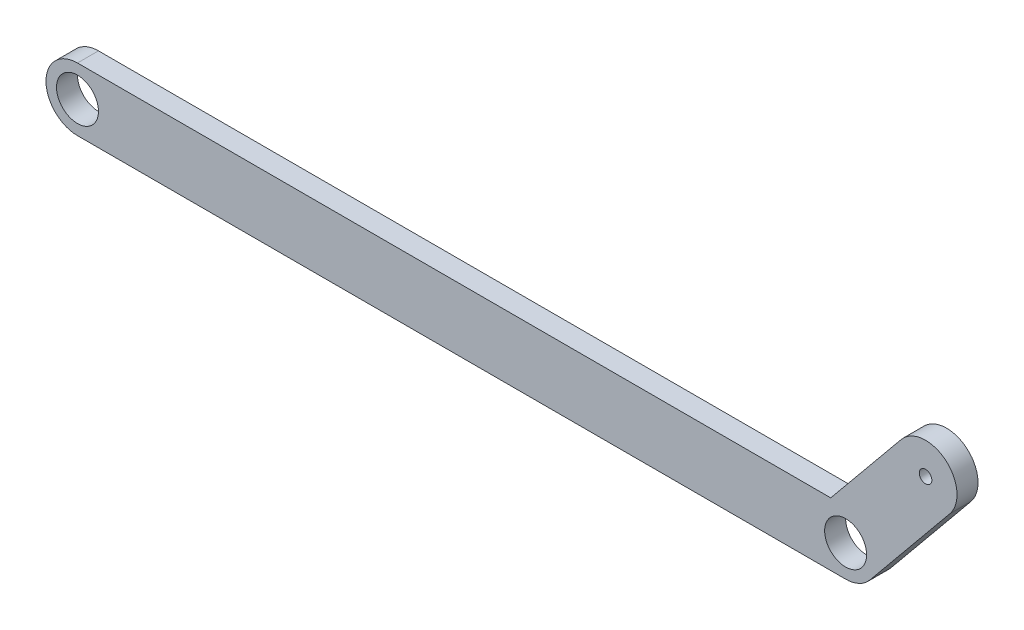
SolidWorks part; units mm, degrees
ref_plane "Front Plane" through (0, 0, 0) normal (0, 0, 1) x (1, 0, 0)
ref_plane "Top Plane" through (0, 0, 0) normal (0, 1, 0) x (1, 0, 0)
ref_plane "Right Plane" through (0, 0, 0) normal (1, 0, 0) x (0, 0, -1)
other "Center of Mass"
sketch "Sketch1" plane through (0, 0, 0) normal (0, 0, 1) x (1, 0, 0)
  line L1 (-46.7941, 9.1438) -> (151.2059, 9.1438)
  line L2 (-46.7941, 9.1438) -> (-46.7941, -5.8562)
  line L3 (-46.7941, -5.8562) -> (151.2059, -5.8562)
  line L4 (151.2059, 9.1438) -> (151.2059, -5.8562)
  dimension "D1" = 15
  dimension "D2" = 198
extrude "Boss-Extrude1" add sketch "Sketch1" along normal blind 5
sketch "Sketch2" plane through (0, 0, 5) normal (0, 0, 1) x (1, 0, 0)
  line L0 (-46.7941, 1.6438) -> (151.2059, 1.6438) construction
  line L1 (-46.7941, 9.1438) -> (-46.7941, -5.8562) construction
  line L2 (151.2059, -5.8562) -> (151.2059, 9.1438) construction
  line L7 (-46.7941, 9.1438) -> (-46.7941, -5.8562)
  line L8 (-46.7941, -5.8562) -> (151.2059, -5.8562)
  line L9 (151.2059, -5.8562) -> (151.2059, 9.1438)
  line L10 (151.2059, 9.1438) -> (-46.7941, 9.1438)
  line L11 (-46.7941, 9.1438) -> (-46.7941, -5.8562)
  line L12 (-46.7941, -5.8562) -> (151.2059, -5.8562)
  line L13 (151.2059, -5.8562) -> (151.2059, 9.1438)
  line L14 (151.2059, 9.1438) -> (-46.7941, 9.1438)
  circle A0 centre (-39.2941, 1.6438) radius 7.5
  circle A1 centre (143.7059, 1.6438) radius 7.5
  circle A2 centre (-39.2941, 1.6438) radius 5
  circle A3 centre (143.7059, 1.6438) radius 5
  line M7 (-46.7941, 9.1438) -> (-46.7941, -5.8562)
  line M8 (-46.7941, -5.8562) -> (151.2059, -5.8562)
  line M9 (151.2059, -5.8562) -> (151.2059, 9.1438)
  line M10 (151.2059, 9.1438) -> (-46.7941, 9.1438)
  dimension "D1" = 7.5
  dimension "D3" = 0
  dimension "D2" = 7.5
extrude "Cut-Extrude1" cut sketch "Sketch2" against normal through all contours A2 L0 | L0 A2 | A0 L14 M7 | A0 L11 M8 | A3 L0 | L0 A3 | A1 L13 M10 | A1 M8 M9
sketch "Sketch3" plane through (0, 0, 5) normal (0, 0, 1) x (1, 0, 0)
  line L0 (149.5018, -3.1162) -> (168.5418, 20.0674)
  line L2 (156.9501, 29.5874) -> (140.1603, 9.1438)
  line L3 (143.7059, 9.1438) -> (-39.2941, 9.1438) construction
  arc A0 (143.7059, -5.8562) -> (143.7059, 9.1438) centre (143.7059, 1.6438) ccw construction
  circle A1 centre (162.746, 24.8274) radius 1.5
  arc A2 (168.5418, 20.0674) -> (156.9501, 29.5874) centre (162.746, 24.8274) ccw
  circle A3 centre (143.7059, 1.6438) radius 5 construction
  arc M6 (143.7059, -5.8562) -> (143.7059, 9.1438) centre (143.7059, 1.6438) ccw
  line M7 (143.7059, 9.1438) -> (-39.2941, 9.1438)
  dimension "D1" = 3
  dimension "D2" = 30
extrude "Boss-Extrude2" add sketch "Sketch3" against normal blind 5 contours L0 A2 L2 A1 M7 M6
